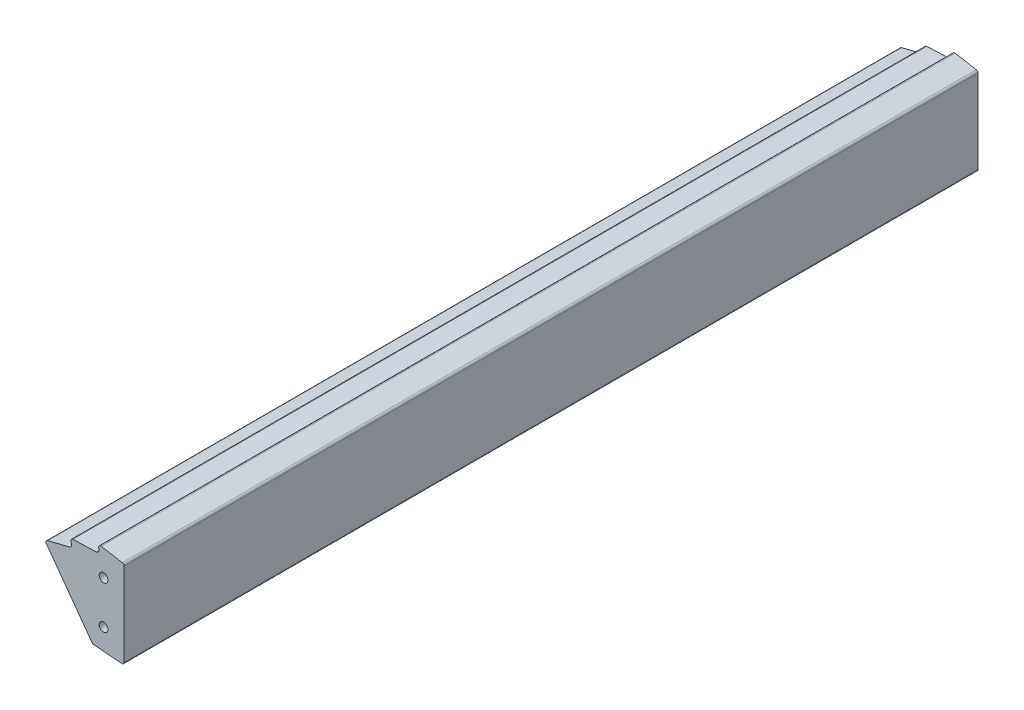
SolidWorks part; units mm, degrees
material "ladder carbon corrected"
ref_plane "Front Plane" through (0, 0, 0) normal (0, 0, 1) x (1, 0, 0)
ref_plane "Top Plane" through (0, 0, 0) normal (0, 1, 0) x (1, 0, 0)
ref_plane "Right Plane" through (0, 0, 0) normal (1, 0, 0) x (0, 0, -1)
sketch "Sketch1" plane through (0, 0, 0) normal (0, 0, 1) x (1, 0, 0)
  line L0 (-19.1269, 28.9196) -> (-2.6193, 27.602)
  line L1 (-46.8997, 66.2532) -> (-20.221, 29.5332)
  line L2 (-46.0481, 68.5905) -> (-33.2024, 71.7845)
  line L3 (-31.1768, 76.652) -> (-17.552, 77.119)
  line L4 (-1, 77.8014) -> (-1, 29.0973)
  line L5 (-14.5587, 81.459) -> (-2.2386, 79.2785)
  line L6 (0, 0) -> (-21.3966, 104.6618) construction
  line L7 (0, 0) -> (-41.6883, 95.6295) construction
  line L8 (-19.7813, 28.3232) -> (5.0398, 26.3421) construction
  line L9 (0, 0) -> (2.1211, 26.575) construction
  line L10 (-30.1863, 29.8023) -> (12.2556, 26.4148) construction
  line L11 (-19.7813, 28.3232) -> (-19.7378, 28.868) construction
  line L12 (-46.4094, 27.8735) -> (21.976, 24.7628) construction
  line L13 (0, 0) -> (0, 116.6603) construction
  line L15 (0, 0) -> (-56.299, 77.489) construction
  line L19 (-16.2897, 79.6815) -> (-16.1338, 78.9186)
  line L20 (-32.5005, 74.5535) -> (-32.1893, 73.8396)
  arc A0 (-33.2024, 71.7845) -> (-32.1893, 73.8396) centre (-33.5643, 73.2402) ccw
  arc A1 (-31.1768, 76.652) -> (-32.5005, 74.5535) centre (-31.1255, 75.1529) ccw
  arc A2 (-17.552, 77.119) -> (-16.1338, 78.9186) centre (-17.6034, 78.6181) ccw
  arc A3 (-14.5587, 81.459) -> (-16.2897, 79.6815) centre (-14.8201, 79.982) ccw
  arc A4 (-2.2386, 79.2785) -> (-1, 77.8014) centre (-2.5, 77.8014) cw
  arc A5 (-46.0481, 68.5905) -> (-46.8997, 66.2532) centre (-45.6861, 67.1348) ccw
  arc A6 (-19.1269, 28.9196) -> (-20.221, 29.5332) centre (-19.0075, 30.4148) cw
  arc A7 (-1, 29.0973) -> (-2.6193, 27.602) centre (-2.5, 29.0973) cw
  circle A8 centre (0, 0) radius 77.675 construction
  dimension "D1" = 1.5
  dimension "D2" = 1.5
  dimension "D11" = 155.35
  dimension "D3" = 2.928
  dimension "D4" = 26.6595
  dimension "D5" = 27.3061
  dimension "D6" = 24.9
  dimension "D7" = 0.5466
  dimension "D8" = 36
  dimension "D9" = 85.437
  dimension "D10" = 1
  dimension "D12" = 11.554
  dimension "D13" = 12
  dimension "D14" = 79.963
  dimension "D15" = 12
  dimension "D16" = 12
extrude "Extrude-Thin1" add sketch "Sketch1" along normal blind 137.5002 and the other way blind 213.5 thin thin type one direction reverse wall 0.27
sketch "Sketch2" plane through (0, 0, 0) normal (0, 0, 1) x (1, 0, 0)
  line L0 (-46.6812, 66.4119) -> (-20.0026, 29.6919) construction
  line L1 (-19.1054, 29.1887) -> (-2.5979, 27.8712) construction
  line L2 (-1.27, 29.0973) -> (-1.27, 77.8014) construction
  line L3 (-46.6812, 66.4119) -> (-20.0026, 29.6919)
  line L4 (-19.1054, 29.1887) -> (-2.5979, 27.8712)
  line L5 (-1.27, 29.0973) -> (-1.27, 77.8014)
  line L6 (-46.6812, 66.4119) -> (-46.7308, 66.48)
  line L31 (-1.27, 77.9505) -> (-1.27, 77.8014)
  line L36 (-2.2638, 79.1357) -> (-14.584, 81.3162)
  line L37 (-16.1477, 79.7106) -> (-15.9917, 78.9476)
  line L38 (-17.547, 76.9741) -> (-31.1719, 76.5071)
  line L39 (-32.3676, 74.6114) -> (-32.0564, 73.8976)
  line L40 (-33.1674, 71.6438) -> (-46.0131, 68.4498)
  line L41 (-2.2638, 79.1357) -> (-14.584, 81.3162)
  line L42 (-16.1477, 79.7106) -> (-15.9917, 78.9476)
  line L43 (-17.547, 76.9741) -> (-31.1719, 76.5071)
  line L44 (-32.3676, 74.6114) -> (-32.0564, 73.8976)
  line L45 (-33.1674, 71.6438) -> (-46.0131, 68.4498)
  arc A0 (-20.0026, 29.6919) -> (-19.1054, 29.1887) centre (-19.0075, 30.4148) ccw construction
  arc A1 (-2.5979, 27.8712) -> (-1.27, 29.0973) centre (-2.5, 29.0973) ccw construction
  arc A2 (-20.0026, 29.6919) -> (-19.1054, 29.1887) centre (-19.0075, 30.4148) ccw
  arc A3 (-2.5979, 27.8712) -> (-1.27, 29.0973) centre (-2.5, 29.0973) ccw
  arc A24 (-46.0131, 68.4498) -> (-46.7308, 66.48) centre (-45.7081, 67.2231) ccw
  arc A25 (-2.2638, 79.1357) -> (-1.27, 77.9505) centre (-2.4736, 77.9505) cw
  arc A28 (-14.584, 81.3162) -> (-16.1477, 79.7106) centre (-14.8201, 79.982) ccw
  arc A29 (-17.547, 76.9741) -> (-15.9917, 78.9476) centre (-17.6034, 78.6181) ccw
  arc A30 (-31.1719, 76.5071) -> (-32.3676, 74.6114) centre (-31.1255, 75.1529) ccw
  arc A31 (-33.1674, 71.6438) -> (-32.0564, 73.8976) centre (-33.5643, 73.2402) ccw
  arc A32 (-14.584, 81.3162) -> (-16.1477, 79.7106) centre (-14.8201, 79.982) ccw
  arc A33 (-17.547, 76.9741) -> (-15.9917, 78.9476) centre (-17.6034, 78.6181) ccw
  arc A34 (-31.1719, 76.5071) -> (-32.3676, 74.6114) centre (-31.1255, 75.1529) ccw
  arc A35 (-33.1674, 71.6438) -> (-32.0564, 73.8976) centre (-33.5643, 73.2402) ccw
  dimension "D1" = 0.125
extrude "Boss-Extrude1" add sketch "Sketch2" along normal offset from surface 75 and the other way offset from surface (288.5 mm away) 75 separate body up to face at (-20.8113, 63.8316, 137.5002) offset beyond the face yes other way up to face at (-20.725, 63.7904, -213.5)
delete or keep bodies "Body-Delete1" type delete bodies bodies 101
sketch "Sketch3" plane through (0, 0, 0) normal (1, 0, 0) x (0, 0, -1)
  line L0 (-212.0001, 103.5239) -> (287.9999, 103.5239)
  line L1 (-212.0001, 103.5239) -> (-212.0001, 3.5239)
  line L2 (287.9999, 103.5239) -> (287.9999, 3.5239)
  line L3 (-212.0001, 3.5239) -> (287.9999, 3.5239)
  line L4 (-212.5003, 53.5239) -> (-212.0001, 53.5239) construction
  line L5 (-212.5003, 29.0973) -> (-212.5002, 77.9505) construction
  line L6 (288.5, 53.5239) -> (287.9999, 53.5239) construction
  line L7 (288.5, 77.9505) -> (288.5, 29.0973) construction
  dimension "D1" = 500
  dimension "D2" = 100
extrude "Cut-Extrude1" cut sketch "Sketch3" against normal through all flip side to cut
hole_wizard "1/4-20 Tapped Hole1" positions "3DSketch1" profile "Sketch4" tap size "1/4-20" standard "ANSI Inch"
sketch3d "3DSketch1"
  line L0 (-13.27, 66.0239, -287.9999) -> (-13.27, 41.0239, -287.9999)
  line L1 (-13.27, 41.0239, -287.9999) -> (-13.27, 41.0239, 212.0001)
  line L2 (-13.27, 41.0239, 212.0001) -> (-13.27, 66.0239, 212.0001)
  line L3 (-13.27, 66.0239, 212.0001) -> (-13.27, 66.0239, -287.9999)
  line L6 (-1.27, 29.0973, 212.0001) -> (-1.27, 77.9505, 212.0001) construction
  line L8 (-13.27, 53.5239, -287.9999) -> (-1.27, 53.5239, -287.9999) construction
  line L10 (-1.27, 77.9505, -287.9999) -> (-1.27, 29.0973, -287.9999) construction
  point P0 (-13.27, 66.0239, 212.0001)
  point P2 (-13.27, 41.0239, 212.0001)
  point P4 (-13.27, 66.0239, -287.9999)
  point P6 (-13.27, 41.0239, -287.9999)
  dimension "D1" = 25
  dimension "D2" = 12
sketch "Sketch4" plane through (-13.27, 66.0239, 212.0001) normal (1, 0, 0) x (0, -1, 0)
  line L0 (0, 0) -> (0, 18.0438)
  line L1 (0, 18.0438) -> (2.5527, 16.51)
  line L2 (2.5527, 16.51) -> (2.5527, 0)
  line L5 (2.5527, 0) -> (0, 0)
  line L10 (0, 18.0438) -> (-2.5527, 16.51) construction
  line L11 (0, -6.35) -> (0, 107.95) construction
  dimension "Tap Drill Dia." = 5.1054
  dimension "Tap Drill Depth" = 16.51
  dimension "Drill Angle" = 118
cosmetic thread "Hole Thread1" parameters "D1"=12.7, "D2"=6.35
cosmetic thread "Hole Thread2" parameters "D1"=12.7, "D2"=6.35
cosmetic thread "Hole Thread3" parameters "D1"=12.7, "D2"=6.35
cosmetic thread "Hole Thread4" parameters "D1"=12.7, "D2"=6.35
